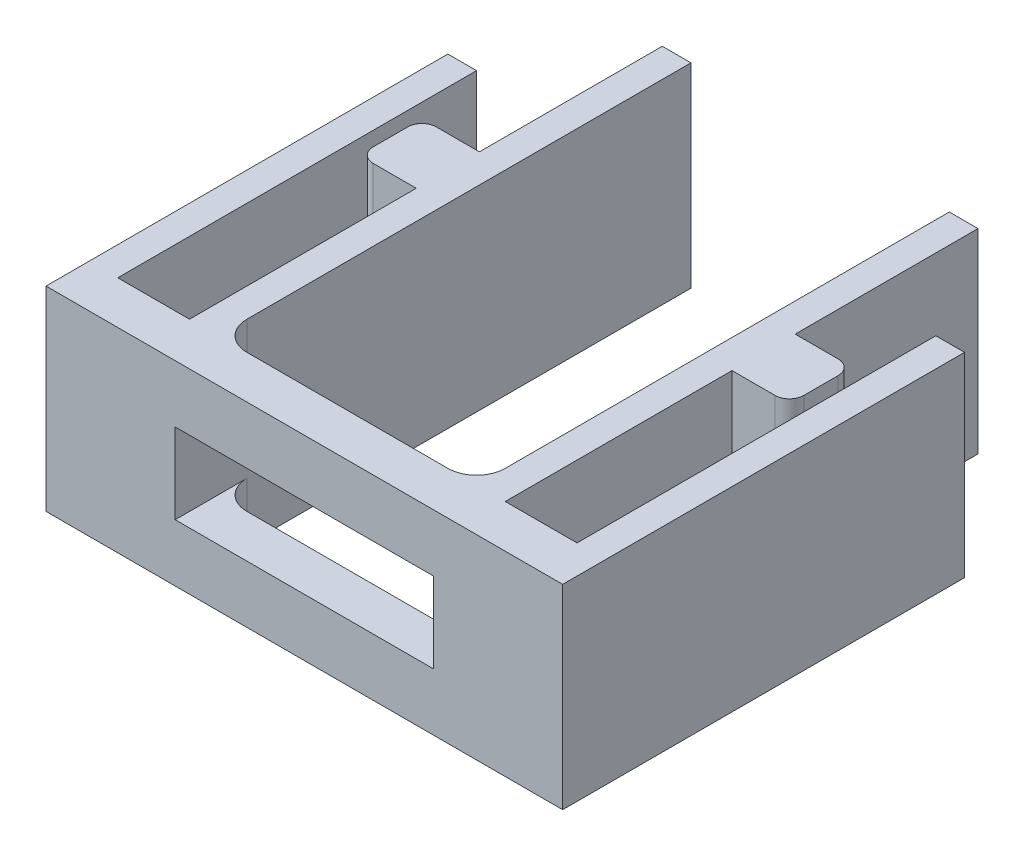
SolidWorks part; units mm, degrees
ref_plane "Alzado" through (0, 0, 0) normal (0, 0, 1) x (1, 0, 0)
ref_plane "Planta" through (0, 0, 0) normal (0, 1, 0) x (1, 0, 0)
ref_plane "Vista lateral" through (0, 0, 0) normal (1, 0, 0) x (0, 0, -1)
sketch "Croquis1" plane through (0, 0, 0) normal (0, 1, 0) x (1, 0, 0)
  line L0 (0, 0) -> (0, 14)
  line L1 (0, 14) -> (1, 14)
  line L2 (1, 14) -> (17, 14) construction
  line L3 (13.5, 17.9697) -> (4.5, 17.9697) construction
  line L4 (3.5, 1.5) -> (3.5, 9.4)
  line L5 (3.5, 9.4) -> (1.5, 9.4)
  line L6 (1, 14) -> (1, 1.5)
  line L7 (1, 1.5) -> (3.5, 1.5)
  line L8 (1.5, 9.4) -> (1.5, 11.6)
  line L9 (3.5, 17.9697) -> (4.5, 17.9697)
  line L10 (4.5, 17.9697) -> (4.5, 2.5)
  line L11 (5.5, 1.5) -> (12.5, 1.5)
  line L12 (13.5, 2.5) -> (13.5, 17.9697)
  line L13 (13.5, 17.9697) -> (14.5, 17.9697)
  line L14 (14.5, 17.9697) -> (14.5, 11.6)
  line L15 (14.5, 11.6) -> (16.5, 11.6)
  line L16 (16.5, 11.6) -> (16.5, 9.4)
  line L17 (16.5, 9.4) -> (14.5, 9.4)
  line L18 (14.5, 9.4) -> (14.5, 1.5)
  line L19 (14.5, 1.5) -> (17, 1.5)
  line L20 (17, 1.5) -> (17, 14)
  line L21 (17, 14) -> (18, 14)
  line L22 (18, 14) -> (18, 0)
  line L23 (18, 0) -> (0, 0)
  line L24 (3.5, 1.5) -> (5.5, 1.5) construction
  line L25 (14.5, 1.5) -> (12.5, 1.5) construction
  line L26 (1.5, 11.6) -> (3.5, 11.6)
  line L27 (3.5, 11.6) -> (3.5, 17.9697)
  line L28 (5.5, 2.5) -> (4.5, 2.5) construction
  line L29 (12.5, 2.5) -> (12.5, 1.5) construction
  arc A0 (5.5, 1.5) -> (4.5, 2.5) centre (5.5, 2.5) cw
  arc A1 (12.5, 1.5) -> (13.5, 2.5) centre (12.5, 2.5) ccw
  point P3 (16.5, 10.5)
  dimension "D1" = 2.5
  dimension "D2" = 1
  dimension "D3" = 9
  dimension "D4" = 2.2
  dimension "D5" = 16.5
  dimension "D6" = 2
  dimension "D7" = 12.5
  dimension "D8" = 1.5
  dimension "D9" = 18
  dimension "D10" = 90
  dimension "D11" = 1
  dimension "D12" = 90
extrude "Saliente-Extruir1" add sketch "Croquis1" along normal blind 6.8
sketch "Croquis2" plane through (0, 0, 0) normal (0, 0, 1) x (1, 0, 0)
  line L0 (4.5, 2) -> (4.5, 0) construction
  line L1 (13.5, 2) -> (4.5, 2)
  line L2 (13.5, 2) -> (13.5, 4.8)
  line L3 (13.5, 4.8) -> (4.5, 4.8)
  line L4 (4.5, 2) -> (4.5, 4.8)
  line L5 (13.5, 2) -> (4.5, 4.8) construction
  line L6 (13.5, 4.8) -> (4.5, 2) construction
  line L7 (0, 0) -> (18, 0) construction
  line L8 (4.5, 4.8) -> (4.5, 6.8) construction
  line L9 (0, 6.8) -> (18, 6.8) construction
  line L10 (13.5, 4.8) -> (18, 4.8) construction
  line L11 (18, 6.8) -> (18, 0) construction
  line L12 (4.5, 4.8) -> (0, 4.8) construction
  line L13 (0, 6.8) -> (0, 0) construction
  point P0 (9, 3.4)
  point P19 (7, 3.4)
  dimension "D1" = 2
  dimension "D2" = 4.5
extrude "Cortar-Extruir1" cut sketch "Croquis2" against normal through all
fillet "Redondeo1" radius 0.5 1 edges at (16.5, 3.4, -11.6)
fillet "Redondeo2" radius 0.5 1 edges at (16.5, 3.4, -9.4)
fillet "Redondeo3" radius 0.5 1 edges at (1.5, 3.4, -9.4)
fillet "Redondeo4" radius 0.5 1 edges at (1.5, 3.4, -11.6)
